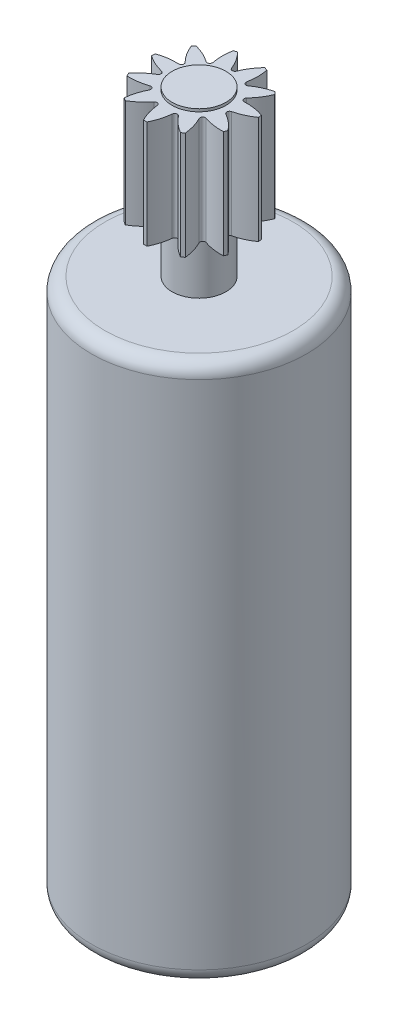
SolidWorks part; units mm, degrees
ref_plane "Front Plane" through (0, 0, 0) normal (0, 0, 1) x (1, 0, 0)
ref_plane "Top Plane" through (0, 0, 0) normal (0, 1, 0) x (1, 0, 0)
ref_plane "Right Plane" through (0, 0, 0) normal (1, 0, 0) x (0, 0, -1)
sketch "Sketch1" plane through (0, 0, 0) normal (0, 0, 1) x (1, 0, 0)
  line L0 (0, 0) -> (0, 26.1)
  line L1 (0, 0) -> (4, 0)
  line L2 (4, 0) -> (4, 20)
  line L3 (4, 20) -> (1, 20)
  line L4 (1, 20) -> (1, 22)
  line L5 (1, 22) -> (2, 22)
  line L6 (2, 22) -> (2, 26)
  line L7 (2, 26) -> (1, 26)
  line L8 (1, 26) -> (1, 26.1)
  line L9 (1, 26.1) -> (0, 26.1)
  dimension "D1" = 26.1
  dimension "D2" = 4
  dimension "D3" = 20
  dimension "D4" = 3
  dimension "D5" = 2
  dimension "D6" = 1
  dimension "D7" = 4
  dimension "D8" = 1
  dimension "D9" = 0.1
revolve "Revolve1" add sketch "Sketch1" angle 360 about L0
fillet "Fillet1" radius 0.5 2 edges at (0, 20, -4) (0, 0, -4)
sketch "Sketch2" plane through (0, 26, 0) normal (0, 1, 0) x (1, 0, 0)
  line L0 (0, 0) -> (0, 5.4977) construction
  arc A0 (-0.5, 1.9365) -> (-0.0929, 1.2999) centre (-1.951, 0.5601) cw
  circle A1 centre (0, 0) radius 2 construction
  circle A2 centre (0, 0) radius 1 construction
  arc A3 (0.0929, 1.2999) -> (0.5, 1.9365) centre (1.951, 0.5601) cw
  arc A4 (0.5, 1.9365) -> (-0.5, 1.9365) centre (0, 0) ccw
  arc A5 (-0.0929, 1.2999) -> (0.0929, 1.2999) centre (0, 1.3369) ccw
  point P12 (0, 0)
  point P15 (0, 1)
  dimension "D2" = 2
  dimension "D3" = 2
  dimension "D4" = 0.1
  dimension "D1" = 1
extrude "Cut-Extrude1" cut sketch "Sketch2" against normal blind 4
pattern_circular "CirPattern1" count 11 over 360 about axis through (0, 0, 0) along (0, 1, 0) of "Cut-Extrude1"
